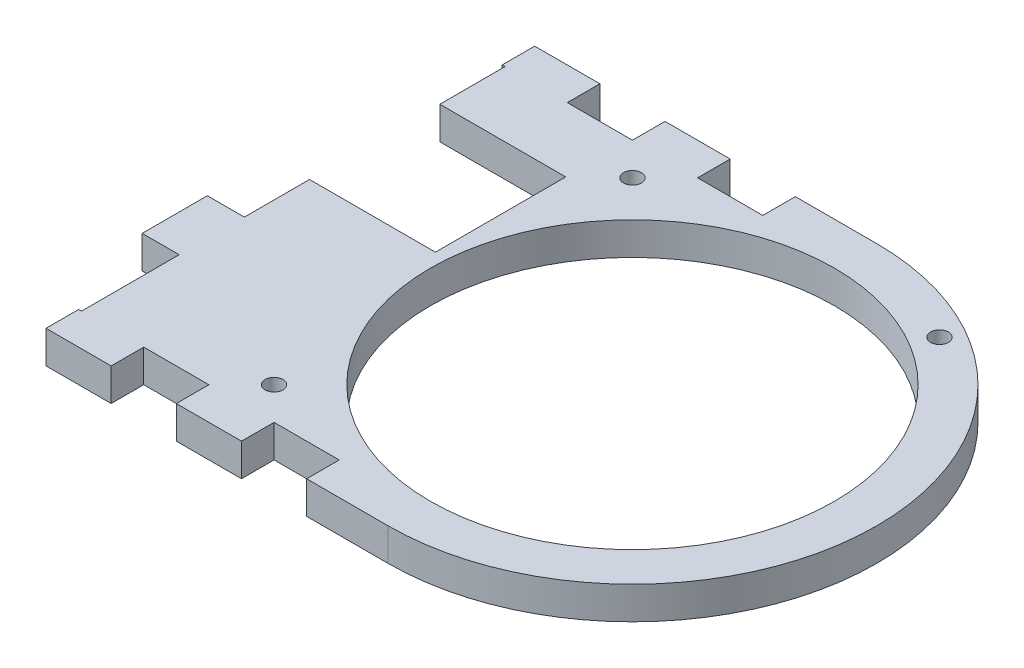
SolidWorks part; units mm, degrees
ref_plane "Front Plane" through (0, 0, 0) normal (0, 0, 1) x (1, 0, 0)
ref_plane "Top Plane" through (0, 0, 0) normal (0, 1, 0) x (1, 0, 0)
ref_plane "Right Plane" through (0, 0, 0) normal (1, 0, 0) x (0, 0, -1)
sketch "Sketch1" plane through (0, 0, 0) normal (0, 0, 1) x (1, 0, 0)
  line L0 (0, 0) -> (40.3547, 419.1) construction
  line L1 (40.3547, 419.1) -> (159.2585, 419.1) construction
  line L2 (159.2585, 419.1) -> (159.2585, 0) construction
  line L3 (159.2585, 0) -> (0, 0) construction
  line L4 (159.2585, -1000) -> (159.2585, 49000) construction
  line L5 (2.0164, 20.9415) -> (40.3547, 419.1) construction
  line L6 (2.0164, 20.9415) -> (41.8323, 17.1077) construction
  line L7 (40.3547, 419.1) -> (80.1706, 415.2662) construction
  line L8 (41.8323, 17.1077) -> (80.1706, 415.2662) construction
  line L9 (64.0085, -1000) -> (64.0085, 49000) construction
  line L10 (-49.0714, 317.5) -> (-124.9206, 324.8034) construction
  line L11 (-26.3513, 414.3375) -> (40.196, 414.3375) construction
  line L12 (-1162.1335, 304.8) -> (48837.8665, 304.8) construction
  line L13 (-126.4915, 292.1) -> (-50.2915, 292.1) construction
  line L14 (-124.9206, 324.8034) -> (-50.2915, 292.1) construction
  line L15 (-49.0714, 317.5) -> (-126.4915, 292.1) construction
  line L16 (40.196, 338.1375) -> (-26.3513, 338.1375) construction
  line L17 (-134.4017, 325.7164) -> (29.8401, 309.9017)
  line L18 (-134.4017, 325.7164) -> (-133.7931, 332.0371)
  line L19 (-133.7931, 332.0371) -> (40.3547, 419.1)
  line L20 (40.3547, 419.1) -> (108.4585, 419.1)
  line L21 (108.4585, 419.1) -> (108.4585, 0) construction
  line L22 (29.8401, 309.9017) -> (0.4102, 4.2603)
  line L23 (0.4102, 4.2603) -> (44.6556, 0)
  line L24 (44.6556, 0) -> (108.4585, 0)
  line L25 (108.4585, 419.1) -> (159.2585, 311.15)
  line L26 (159.2585, 311.15) -> (159.2585, 304.8)
  line L27 (159.2585, 304.8) -> (108.4585, 280.8941)
  line L28 (108.4585, 280.8941) -> (108.4585, 0)
  line L29 (0.4102, 4.2603) -> (1.6331, 16.9603)
  line L30 (0.4102, 4.2603) -> (44.9044, -0.024)
  line L31 (1.6331, 16.9603) -> (46.1273, 12.676)
  line L32 (44.9044, -0.024) -> (46.1273, 12.676)
  arc A0 (-124.9206, 324.8034) -> (-26.3513, 414.3375) centre (-26.3513, 315.3123) cw construction
  arc A1 (73.5335, 304.8) -> (40.196, 338.1375) centre (40.196, 304.8) ccw construction
  arc A2 (149.7335, 304.8) -> (40.196, 414.3375) centre (40.196, 304.8) ccw construction
  arc A3 (-49.0714, 317.5) -> (-26.3513, 338.1375) centre (-26.3513, 315.3123) cw construction
  point P7 (57.6585, 400.05)
  point P10 (45.5182, 6.35)
  point P17 (149.7335, 304.8)
  point P18 (73.5335, 304.8)
  dimension "D9" = 9.525
  dimension "D14" = 25.4
  dimension "D1" = 419.1
  dimension "D2" = 101.6
  dimension "D3" = 19.05
  dimension "D4" = 19.05
  dimension "D5" = 84.5
  dimension "D6" = 40
  dimension "D7" = 400
  dimension "D8" = 95.25
  dimension "D10" = 9.525
  dimension "D11" = 114.3
  dimension "D12" = 76.2
  dimension "D13" = 9.525
  dimension "D15" = 127
  dimension "D16" = 9.525
  dimension "D17" = 209.55
  dimension "D18" = 6.35
  dimension "D19" = 50.8
  dimension "D20" = 44.45
  dimension "D21" = 6.35
  dimension "D22" = 44.7
  dimension "D23" = 12.7
  dimension "D24" = 6.35
sketch "Sketch2" plane through (0, 0, 0) normal (0, 0, 1) x (1, 0, 0)
  line L1 (159.2585, 0) -> (38.3056, 0)
  line L2 (159.2585, 0) -> (159.2585, 6.35)
  line L3 (159.2585, 6.35) -> (38.3056, 6.35)
  line L4 (38.3056, 0) -> (38.3056, 6.35)
  dimension "D1" = 6.35
  dimension "D2" = 6.35
extrude "Boss-Extrude1" add sketch "Sketch2" along normal blind 95.25
sketch "Sketch3" plane through (0, 6.35, 0) normal (0, 1, 0) x (1, 0, 0)
  line L0 (159.2585, -47.625) -> (111.6335, -47.625) construction
  line L1 (159.2585, -95.25) -> (159.2585, 0) construction
  circle A0 centre (111.6335, -47.625) radius 39.37
  dimension "D1" = 78.74
  dimension "D2" = 47.625
extrude "Cut-Extrude2" cut sketch "Sketch3" against normal through all
sketch "Sketch4" plane through (0, 6.35, 0) normal (0, 1, 0) x (1, 0, 0)
  line L0 (159.2585, -95.25) -> (38.3056, -95.25) construction
  line L1 (-201162.1335, 0) -> (248837.8665, 0) construction
  line L2 (111.6335, -95.25) -> (179.0514, -95.25)
  line L3 (179.0514, -95.25) -> (179.0514, 0)
  line L4 (179.0514, 0) -> (111.6335, 0)
  arc A0 (111.6335, -95.25) -> (111.6335, 0) centre (111.6335, -47.625) ccw
extrude "Cut-Extrude3" cut sketch "Sketch4" against normal through all
sketch "Sketch5" plane through (0, 6.35, 0) normal (0, 1, 0) x (1, 0, 0)
  line L0 (38.3056, -95.25) -> (38.3056, 0) construction
  line L1 (38.3056, -19.05) -> (70.0556, -19.05)
  line L2 (38.3056, -19.05) -> (38.3056, -44.45)
  line L3 (38.3056, -44.45) -> (70.0556, -44.45)
  line L4 (70.0556, -19.05) -> (70.0556, -44.45)
  line L5 (70.0556, -31.75) -> (70.0556, 0) construction
  line L6 (111.6335, 0) -> (38.3056, 0) construction
  dimension "D1" = 31.75
  dimension "D2" = 25.4
  dimension "D3" = 31.75
extrude "Cut-Extrude4" cut sketch "Sketch5" against normal through all
sketch "Sketch6" plane through (0, 6.35, 0) normal (0, 1, 0) x (1, 0, 0)
  line L0 (111.6335, 0) -> (38.3056, 0) construction
  line L1 (95.7585, 0) -> (83.0585, 0)
  line L2 (95.7585, 0) -> (95.7585, -6.35)
  line L3 (95.7585, -6.35) -> (83.0585, -6.35)
  line L4 (83.0585, 0) -> (83.0585, -6.35)
  line L5 (111.6335, -95.25) -> (38.3056, -95.25) construction
  line L6 (83.0585, -95.25) -> (95.7585, -95.25)
  line L7 (83.0585, -95.25) -> (83.0585, -88.9)
  line L8 (83.0585, -88.9) -> (95.7585, -88.9)
  line L9 (95.7585, -95.25) -> (95.7585, -88.9)
  dimension "D1" = 12.7
  dimension "D2" = 12.7
  dimension "D3" = 6.35
extrude "Cut-Extrude5" cut sketch "Sketch6" against normal through all
pattern_linear "LPattern1" count 3 spacing 25.4 along (-1, 0, 0) of "Cut-Extrude5"
sketch "Sketch7" plane through (0, 6.35, 0) normal (0, 1, 0) x (1, 0, 0)
  line L0 (70.0556, -19.05) -> (38.3056, -19.05) construction
  line L1 (38.3056, -6.35) -> (45.5182, -6.35)
  line L2 (38.3056, -6.35) -> (38.3056, -19.05)
  line L3 (38.3056, -19.05) -> (45.5182, -19.05)
  line L4 (45.5182, -6.35) -> (45.5182, -19.05)
  line L5 (38.3056, -88.9) -> (38.3056, -44.45) construction
  line L6 (38.3056, -88.9) -> (45.5182, -88.9)
  line L7 (38.3056, -88.9) -> (38.3056, -69.85)
  line L8 (38.3056, -69.85) -> (45.5182, -69.85)
  line L9 (45.5182, -88.9) -> (45.5182, -69.85)
  line L10 (38.3056, -57.15) -> (45.5182, -57.15)
  line L11 (38.3056, -57.15) -> (38.3056, -44.45)
  line L12 (38.3056, -44.45) -> (45.5182, -44.45)
  line L13 (45.5182, -57.15) -> (45.5182, -44.45)
  line L14 (38.3056, -44.45) -> (70.0556, -44.45) construction
  line L15 (57.6585, -95.25) -> (44.9585, -95.25) construction
  dimension "D1" = 25.4
  dimension "D2" = 12.7
extrude "Cut-Extrude6" cut sketch "Sketch7" against normal through all
sketch "Sketch8" plane through (0, 6.35, 0) normal (0, 1, 0) x (1, 0, 0)
  line L1 (146.5585, -82.55) -> (76.7085, -82.55) construction
  line L2 (146.5585, -82.55) -> (146.5585, -12.7) construction
  line L3 (146.5585, -12.7) -> (76.7085, -12.7) construction
  line L4 (76.7085, -82.55) -> (76.7085, -12.7) construction
  line L5 (146.5585, -82.55) -> (76.7085, -12.7) construction
  line L6 (146.5585, -12.7) -> (76.7085, -82.55) construction
  circle A0 centre (76.7085, -12.7) radius 1.75
  circle A1 centre (76.7085, -82.55) radius 1.75
  point P0 (111.6335, -47.625)
  dimension "D2" = 3.5
  dimension "D1" = 69.85
extrude "Cut-Extrude7" cut sketch "Sketch8" against normal through all
sketch "Sketch10" plane through (0, 6.35, 0) normal (0, 1, 0) x (1, 0, 0)
  line L0 (111.6335, -47.625) -> (135.446, -6.3805) construction
  line L1 (70.0556, -44.45) -> (70.0556, -19.05) construction
  arc A0 (111.6335, -95.25) -> (111.6335, 0) centre (111.6335, -47.625) ccw construction
  circle A1 centre (133.541, -9.6801) radius 1.75
  dimension "D3" = 3.5
  dimension "D1" = 30
  dimension "D2" = 3.81
extrude "Cut-Extrude9" cut sketch "Sketch10" against normal through all
